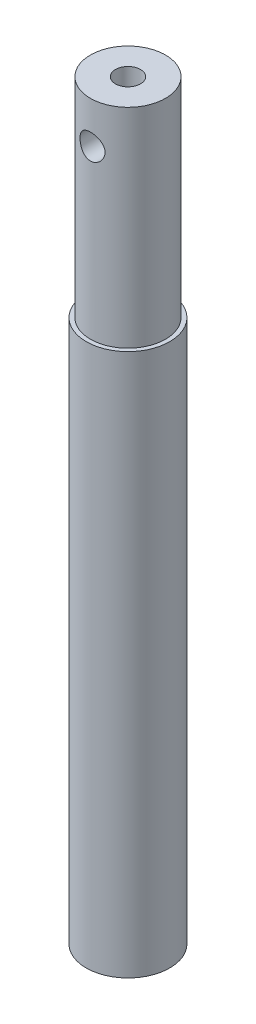
SolidWorks part; units mm, degrees
ref_plane "Front" through (0, 0, 0) normal (0, 0, 1) x (1, 0, 0)
ref_plane "Top" through (0, 0, 0) normal (0, 1, 0) x (1, 0, 0)
ref_plane "Right" through (0, 0, 0) normal (1, 0, 0) x (0, 0, -1)
sketch "Sketch1" plane through (0, 0, 0) normal (0, 1, 0) x (1, 0, 0)
  circle A0 centre (0, 0) radius 5
  circle A1 centre (0, 0) radius 2.5
  dimension "D1" = 10
  dimension "D2" = 5
extrude "Boss-Extrude1" add sketch "Sketch1" along normal blind 65
sketch "Sketch2" plane through (0, 65, 0) normal (0, 1, 0) x (1, 0, 0)
  circle A0 centre (0, 0) radius 4.5
  circle A1 centre (0, 0) radius 1.5
  dimension "D1" = 9
  dimension "D2" = 3
extrude "Boss-Extrude2" add sketch "Sketch2" along normal blind 25
sketch "Sketch4" plane through (0, 0, 0) normal (0, 0, 1) x (1, 0, 0)
  line L0 (0, 90) -> (0, 85) construction
  line L1 (1.5, 90) -> (-1.5, 90) construction
  circle A0 centre (0, 85) radius 1.5
  dimension "D1" = 3
  dimension "D2" = 5
extrude "Cut-Extrude1" cut sketch "Sketch4" against normal mid plane 65
